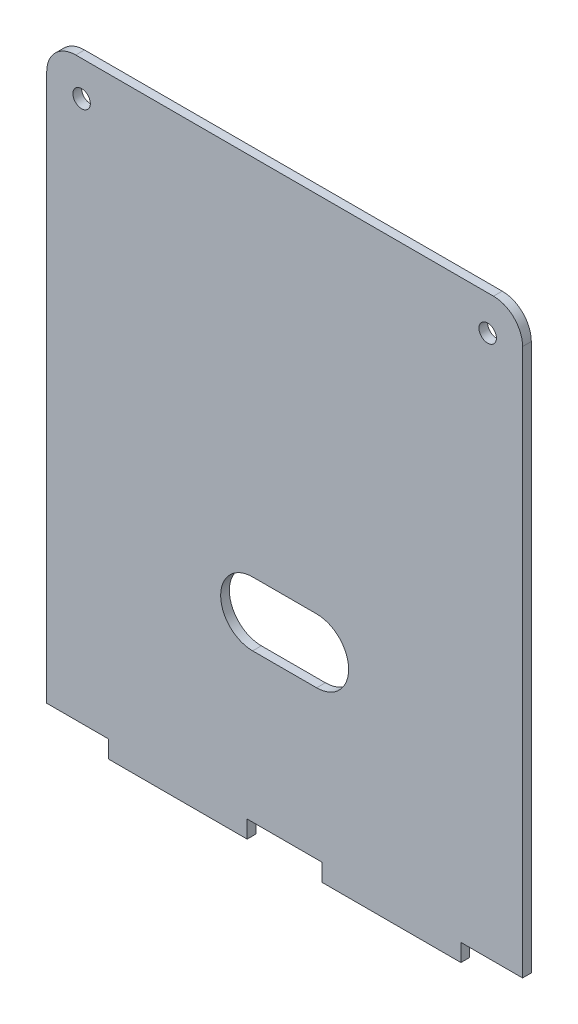
SolidWorks part; units mm, degrees
ref_plane "Front Plane" through (0, 0, 0) normal (0, 0, 1) x (1, 0, 0)
ref_plane "Top Plane" through (0, 0, 0) normal (0, 1, 0) x (1, 0, 0)
ref_plane "Right Plane" through (0, 0, 0) normal (1, 0, 0) x (0, 0, -1)
sketch "Sketch1" plane through (0, 0, 0) normal (0, 0, 1) x (1, 0, 0)
  line L1 (0, 0) -> (81.8, 0)
  line L2 (0, 0) -> (0, 102)
  line L3 (0, 102) -> (81.8, 102)
  line L4 (81.8, 0) -> (81.8, 102)
  dimension "D1" = 81.8
  dimension "D2" = 102
extrude "Boss-Extrude1" add sketch "Sketch1" along normal blind 1.5
sketch "Sketch2" plane through (0, 0, 1.5) normal (0, 0, 1) x (1, 0, 0)
  line L0 (40.9, 102) -> (40.9, 0)
  line L1 (81.8, 102) -> (0, 102) construction
  line L2 (0, 0) -> (81.8, 0) construction
  line L3 (81.8, 0) -> (81.8, 3)
  line L4 (0, 0) -> (10.6, 0)
  line L5 (0, 0) -> (0, 3)
  line L6 (0, 3) -> (10.6, 3)
  line L7 (10.6, 0) -> (10.6, 3)
  line L8 (34.455, 0) -> (47.345, 0)
  line L9 (34.455, 0) -> (34.455, 3)
  line L10 (34.455, 3) -> (47.345, 3)
  line L11 (47.345, 0) -> (47.345, 3)
  line L12 (81.8, 0) -> (71.2, 0)
  line L13 (71.2, 0) -> (71.2, 3)
  line L14 (81.8, 3) -> (71.2, 3)
  line L15 (0, 102) -> (0, 0) construction
  circle A0 centre (6, 96) radius 1.5
  circle A1 centre (75.8, 96) radius 1.5
  line M8 (0, 102) -> (0, 0)
  line M9 (0, 0) -> (81.8, 0)
  line M10 (81.8, 0) -> (81.8, 102)
  dimension "D5" = 6
  dimension "D1" = 3
  dimension "D2" = 10.6
  dimension "D3" = 12.89
  dimension "D4" = 6.445
  dimension "D6" = 6
extrude "Cut-Extrude1" cut sketch "Sketch2" against normal through all contours L7 L6 M9 M8 | L11 L10 L0 M9 | L10 L9 L0 M9 | L14 L13 M10 M9 | A0 | A1
sketch "Sketch3" plane through (0, 0, 1.5) normal (0, 0, 1) x (1, 0, 0)
  line L0 (0, 34) -> (81.8, 34)
  line L1 (0, 102) -> (0, 3) construction
  line L2 (81.8, 3) -> (81.8, 102) construction
  line L3 (40.9, 102) -> (40.9, 3)
  line L4 (81.8, 102) -> (0, 102) construction
  line L5 (34.455, 3) -> (47.345, 3) construction
  line L6 (35.4, 39.5) -> (46.4, 39.5)
  line L7 (35.4, 28.5) -> (46.4, 28.5)
  circle A0 centre (35.4, 34) radius 5.5
  circle A1 centre (46.4, 34) radius 5.5
  point P19 (40.9, 28.5)
  point P20 (40.9, 39.5)
  dimension "D1" = 5.5
  dimension "D2" = 11
  dimension "D3" = 68
extrude "Cut-Extrude2" cut sketch "Sketch3" against normal through all contours L0 A0 | L0 A0 | A1 L0 | A1 L0 | A0 L7 L3 | L7 A1 L3 | L3 A1 L6 | A0 L3 L6
fillet "Fillet1" radius 5 2 edges at (0, 102, 0.75) (81.8, 102, 0.75)
